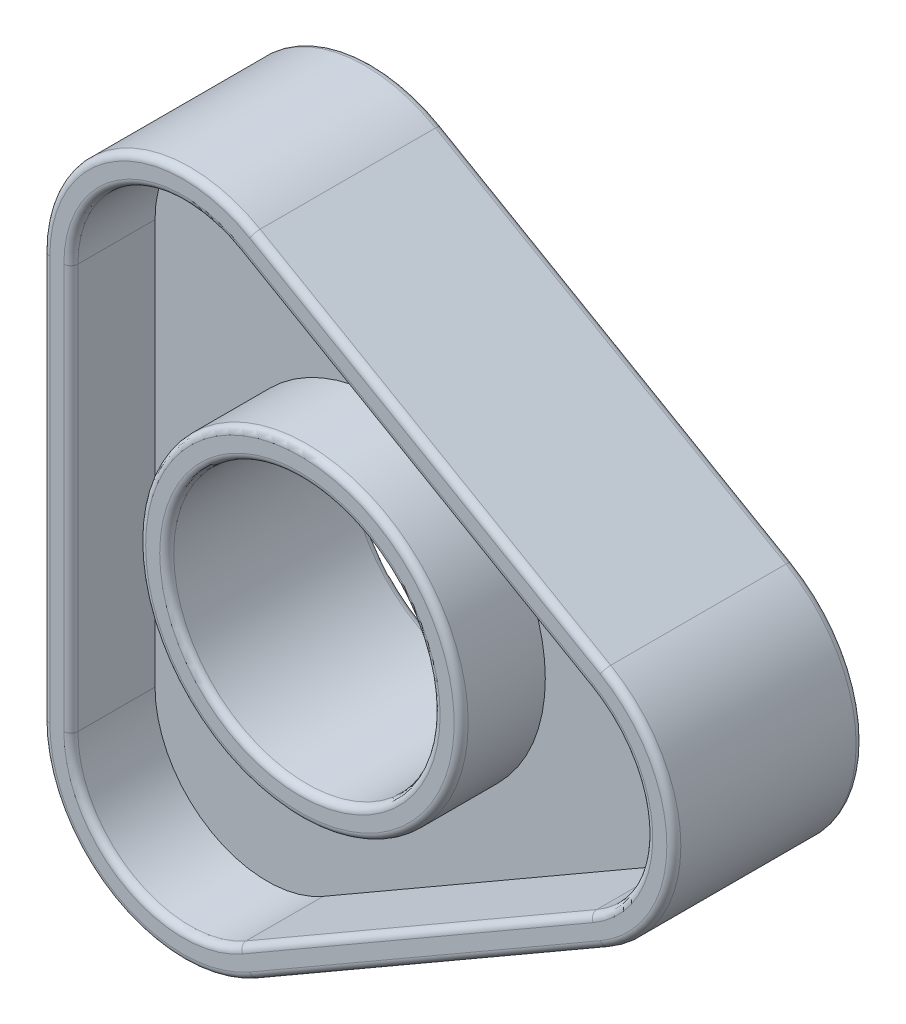
SolidWorks part; units mm, degrees
ref_plane "前基準面" through (0, 0, 0) normal (0, 0, 1) x (1, 0, 0)
ref_plane "上基準面" through (0, 0, 0) normal (0, 1, 0) x (1, 0, 0)
ref_plane "右基準面" through (0, 0, 0) normal (1, 0, 0) x (0, 0, -1)
sketch "草圖1" plane through (0, 0, 0) normal (0, 0, 1) x (1, 0, 0)
  line L1 (21.6667, 8.6603) -> (-3.3333, 23.094)
  line L2 (-18.3333, 14.4338) -> (-18.3333, -14.4338)
  line L3 (-3.3333, -23.094) -> (21.6667, -8.6603)
  circle A0 centre (0, 0) radius 18.3333 construction
  arc A1 (21.6667, 8.6603) -> (21.6667, -8.6603) centre (16.6667, 0) cw
  arc A2 (-18.3333, -14.4338) -> (-3.3333, -23.094) centre (-8.3333, -14.4338) ccw
  arc A3 (-3.3333, 23.094) -> (-18.3333, 14.4338) centre (-8.3333, 14.4338) ccw
  point P1 (0, 0)
  point P9 (36.6667, 0)
  dimension "D2" = 10
  dimension "D1" = 55
extrude "填料-伸長1" add sketch "草圖1" along normal blind 13.5
sketch "草圖2" plane through (0, 0, 13.5) normal (0, 0, 1) x (1, 0, 0)
  line L6 (20.6667, 6.9282) -> (-4.3333, 21.362)
  line L7 (-16.3333, 14.4338) -> (-16.3333, -14.4338)
  line L8 (-4.3333, -21.362) -> (20.6667, -6.9282)
  line L9 (20.6667, 6.9282) -> (-4.3333, 21.362)
  line L10 (-16.3333, 14.4338) -> (-16.3333, -14.4338)
  line L11 (-4.3333, -21.362) -> (20.6667, -6.9282)
  arc A6 (20.6667, -6.9282) -> (20.6667, 6.9282) centre (16.6667, 0) ccw
  arc A7 (-4.3333, 21.362) -> (-16.3333, 14.4338) centre (-8.3333, 14.4338) ccw
  arc A8 (-16.3333, -14.4338) -> (-4.3333, -21.362) centre (-8.3333, -14.4338) ccw
  arc A9 (20.6667, -6.9282) -> (20.6667, 6.9282) centre (16.6667, 0) ccw
  arc A10 (-4.3333, 21.362) -> (-16.3333, 14.4338) centre (-8.3333, 14.4338) ccw
  arc A11 (-16.3333, -14.4338) -> (-4.3333, -21.362) centre (-8.3333, -14.4338) ccw
  dimension "D1" = 2
extrude "除料-伸長1" cut sketch "草圖2" against normal blind 6
sketch "草圖3" plane through (0, 0, 0) normal (0, 0, -1) x (-1, 0, 0)
  line L6 (-20.6667, -6.9282) -> (4.3333, -21.362)
  line L7 (16.3333, -14.4338) -> (16.3333, 14.4338)
  line L8 (4.3333, 21.362) -> (-20.6667, 6.9282)
  line L9 (-20.6667, -6.9282) -> (4.3333, -21.362)
  line L10 (16.3333, -14.4338) -> (16.3333, 14.4338)
  line L11 (4.3333, 21.362) -> (-20.6667, 6.9282)
  arc A6 (-20.6667, 6.9282) -> (-20.6667, -6.9282) centre (-16.6667, 0) ccw
  arc A7 (4.3333, -21.362) -> (16.3333, -14.4338) centre (8.3333, -14.4338) ccw
  arc A8 (16.3333, 14.4338) -> (4.3333, 21.362) centre (8.3333, 14.4338) ccw
  arc A9 (-20.6667, 6.9282) -> (-20.6667, -6.9282) centre (-16.6667, 0) ccw
  arc A10 (4.3333, -21.362) -> (16.3333, -14.4338) centre (8.3333, -14.4338) ccw
  arc A11 (16.3333, 14.4338) -> (4.3333, 21.362) centre (8.3333, 14.4338) ccw
  dimension "D1" = 2
extrude "除料-伸長2" cut sketch "草圖3" against normal blind 6
sketch "草圖4" plane through (0, 0, 7.5) normal (0, 0, 1) x (1, 0, 0)
  circle A0 centre (0, 0) radius 11.5
  dimension "D1" = 23
extrude "填料-伸長2" add sketch "草圖4" along normal up to surface and the other way up to surface
sketch "草圖5" plane through (0, 0, 13.5) normal (0, 0, 1) x (1, 0, 0)
  circle A0 centre (0, 0) radius 9.5
  dimension "D1" = 19
extrude "除料-伸長3" cut sketch "草圖5" against normal up to next
fillet "圓角1" radius 0.5 22 edges at (-12.3333, 21.362, 13.5) (8.1667, 14.1451, 13.5) (24.6667, 0, 13.5) (8.1667, -14.1451, 13.5) (-12.3333, -21.362, 13.5) (-13.3333, 23.094, 13.5) (9.1667, 15.8771, 13.5) (26.6667, 0, 13.5) (9.1667, -15.8771, 13.5) (-13.3333, -23.094, 13.5) (9.1667, 15.8771, 0) (-13.3333, 23.094, 0) (-18.3333, 0, 0) (-13.3333, -23.094, 0) (9.1667, -15.8771, 0) (26.6667, 0, 0) (-11.5, 0, 0) (-9.5, 0, 0) (9.5, 0, 13.5) (-11.5, 0, 13.5) (-16.3333, 0, 13.5) (-18.3333, 0, 13.5)
